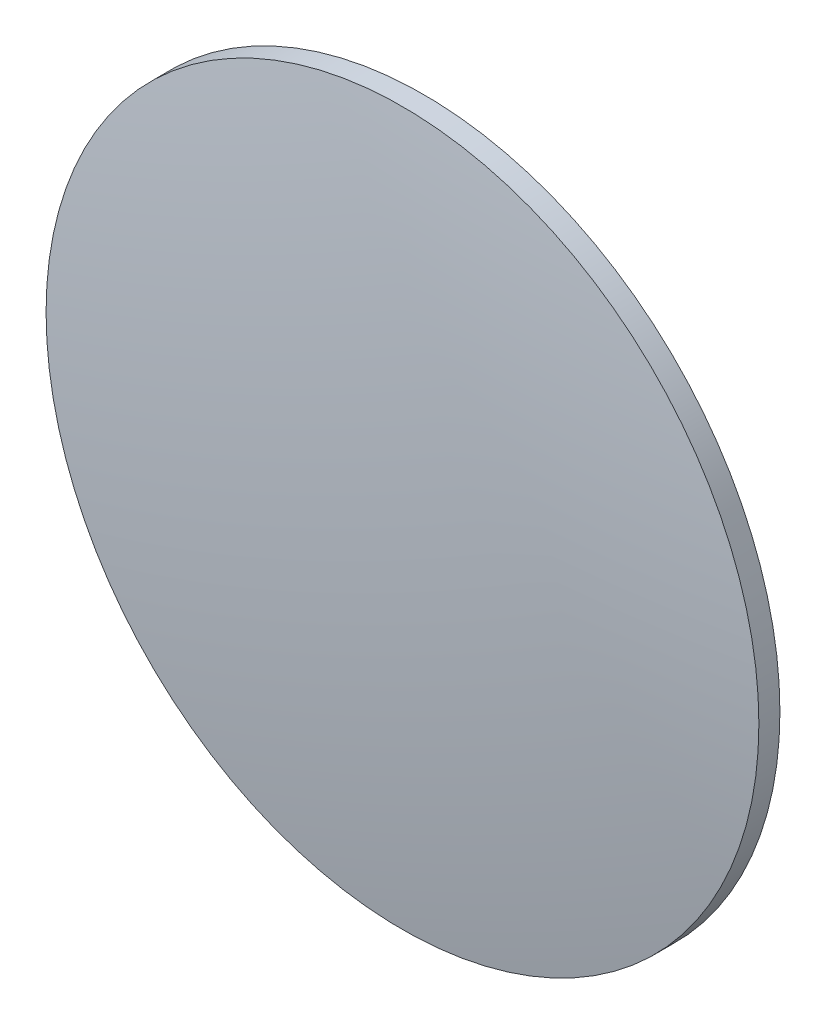
SolidWorks part; units mm, degrees
ref_plane "Front Plane" through (0, 0, 0) normal (0, 0, 1) x (1, 0, 0)
ref_plane "Top Plane" through (0, 0, 0) normal (0, 1, 0) x (1, 0, 0)
ref_plane "Right Plane" through (0, 0, 0) normal (1, 0, 0) x (0, 0, -1)
sketch "Sketch1" plane through (0, 0, 0) normal (0, 0, 1) x (1, 0, 0)
  line L0 (0, 182.571) -> (0, -182.571) construction
  line L1 (0, -200.8281) -> (0, 200.8281) construction
  line L2 (0, 182.571) -> (0, -182.571)
  arc A0 (0, 182.571) -> (0, -182.571) centre (0, 0) ccw
  dimension "D1" = 365.142
revolve "Revolve1" add sketch "Sketch1" angle 360 about L0
ref_plane "Plane1" through (0, 0, 182.571) normal (0, 0, 1) x (1, 0, 0)
sketch "Sketch2" plane through (0, 0, 182.571) normal (0, 0, 1) x (1, 0, 0)
  circle A0 centre (0, 0) radius 25.4
  circle A1 centre (0, 0) radius 182.571
  circle A2 centre (0, 0) radius 182.571 construction
  dimension "D1" = 50.8
  dimension "D2" = 0
extrude "Cut-Extrude1" cut sketch "Sketch2" against normal through all
ref_plane "Plane2" through (0, 0, 179.296) normal (0, 0, 1) x (1, 0, 0)
sketch "Sketch3" plane through (0, 0, 179.296) normal (0, 0, 1) x (1, 0, 0)
  circle A0 centre (0, 0) radius 25.4
extrude "Cut-Extrude3" cut sketch "Sketch3" against normal through all
